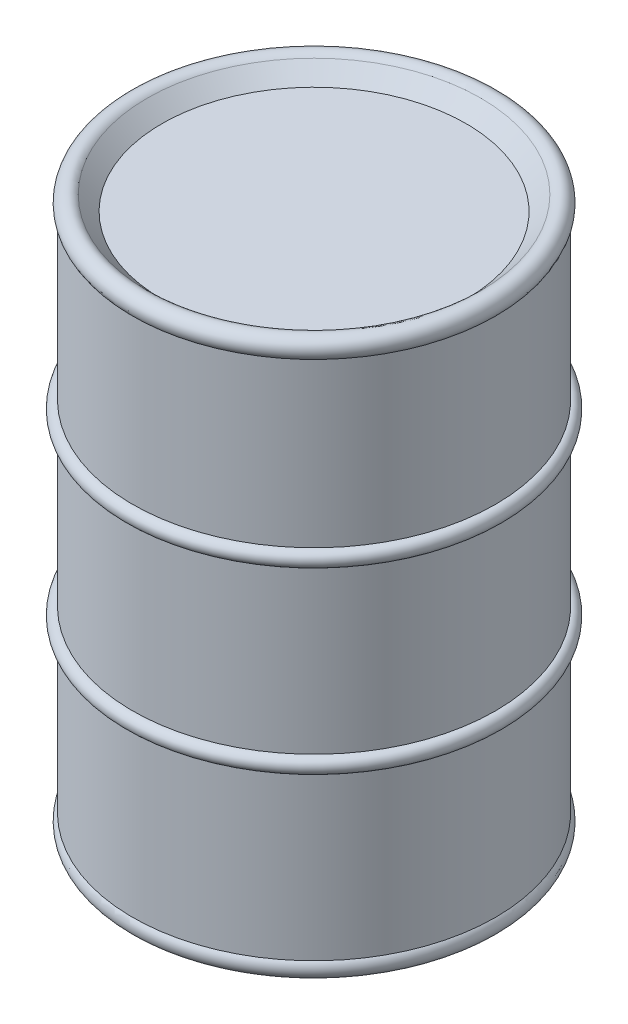
SolidWorks part; units mm, degrees
material "Plain Carbon Steel"
ref_plane "Front Plane" through (0, 0, 0) normal (0, 0, 1) x (1, 0, 0)
ref_plane "Top Plane" through (0, 0, 0) normal (0, 1, 0) x (1, 0, 0)
ref_plane "Right Plane" through (0, 0, 0) normal (1, 0, 0) x (0, 0, -1)
sketch "Sketch1" plane through (0, 0, 0) normal (0, 0, 1) x (1, 0, 0)
  line L1 (292.1, 0) -> (292.1, 262.4667)
  line L2 (292.1, 287.8667) -> (292.1, 550.3333)
  line L3 (292.1, 575.7333) -> (292.1, 838.2)
  line L4 (244.7554, 838.2) -> (0, 838.2)
  line L5 (0, 838.2) -> (0, 837.2881)
  line L6 (0, 837.2881) -> (291.1881, 837.2881)
  line L7 (291.1881, 837.2881) -> (291.1881, 0.9119)
  line L8 (291.1881, 0.9119) -> (0, 0.9119)
  line L9 (0, 0.9119) -> (0, 0)
  line L10 (0, 0.9119) -> (0, 837.2881) construction
  line L12 (244.7554, 838.2) -> (268.4277, 861.8723)
  line L13 (268.4277, -23.6723) -> (244.7554, 0)
  line L14 (244.7554, 0) -> (0, 0)
  line L15 (268.4277, 861.8723) -> (292.1, 838.2) construction
  line L16 (268.4277, -23.6723) -> (292.1, 0) construction
  arc A0 (292.1, 262.4667) -> (292.1, 287.8667) centre (292.1, 275.1667) ccw
  arc A1 (292.1, 550.3333) -> (292.1, 575.7333) centre (292.1, 563.0333) ccw
  arc A3 (292.1, 838.2) -> (268.4277, 861.8723) centre (280.2638, 850.0362) ccw
  arc A4 (292.1, 0) -> (268.4277, -23.6723) centre (280.2638, -11.8362) cw
  point P1 (280.2638, -28.575)
  point P19 (304.8, 275.1667)
  point P30 (280.2638, 866.775)
  dimension "D5" = 895.35
  dimension "D9" = 838.2
  dimension "D1" = 584.2
  dimension "D2" = 0.9119
  dimension "D3" = 609.6
  dimension "D4" = 0.9119
  dimension "D6" = 45
  dimension "D7" = 0.9119
  dimension "D8" = 45
revolve "Revolve1" add sketch "Sketch1" angle 360 about L10
